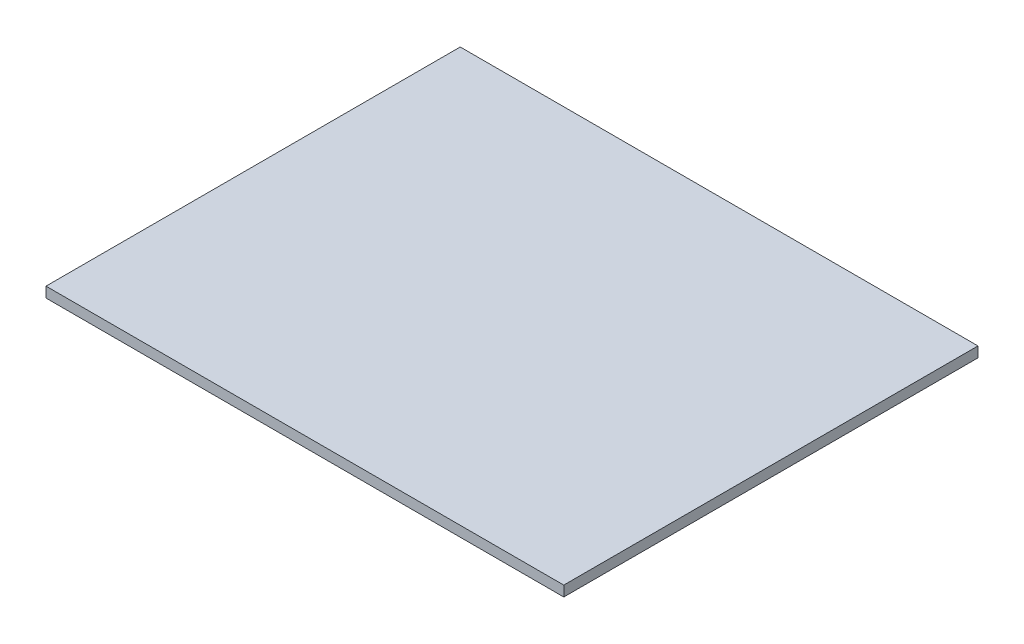
SolidWorks part; units mm, degrees
ref_plane "前视基准面" through (0, 0, 0) normal (0, 0, 1) x (1, 0, 0)
ref_plane "上视基准面" through (0, 0, 0) normal (0, 1, 0) x (1, 0, 0)
ref_plane "右视基准面" through (0, 0, 0) normal (1, 0, 0) x (0, 0, -1)
sketch "草图1" plane through (0, 0, 0) normal (0, 1, 0) x (1, 0, 0)
  line L0 (0, 0) -> (150, 0)
  line L1 (150, 0) -> (150, -120)
  line L2 (150, -120) -> (0, -120)
  line L3 (0, -120) -> (0, 0)
extrude "凸台-拉伸1" add sketch "草图1" along normal blind 3
